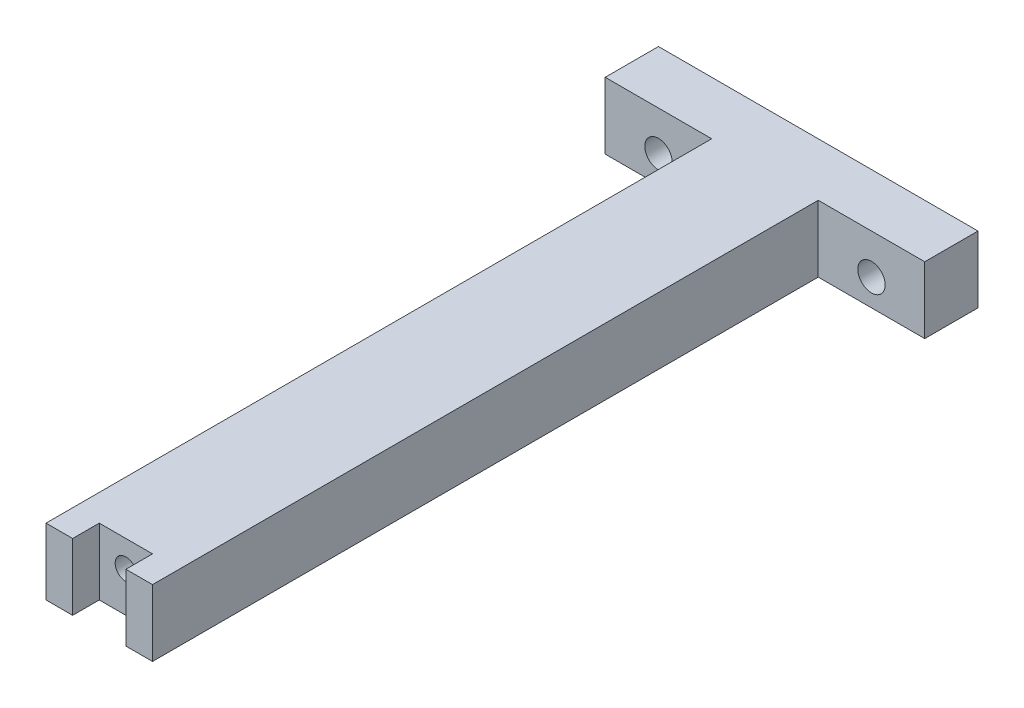
SolidWorks part; units mm, degrees
ref_plane "Front Plane" through (0, 0, 0) normal (0, 0, 1) x (1, 0, 0)
ref_plane "Top Plane" through (0, 0, 0) normal (0, 1, 0) x (1, 0, 0)
ref_plane "Right Plane" through (0, 0, 0) normal (1, 0, 0) x (0, 0, -1)
sketch "Sketch1" plane through (0, 0, 0) normal (0, 0, 1) x (1, 0, 0)
  line L1 (-38.1, -7.9375) -> (38.1, -7.9375)
  line L2 (-38.1, -7.9375) -> (-38.1, 7.9375)
  line L3 (-38.1, 7.9375) -> (38.1, 7.9375)
  line L4 (38.1, -7.9375) -> (38.1, 7.9375)
  line L5 (-38.1, -7.9375) -> (38.1, 7.9375) construction
  line L6 (-38.1, 7.9375) -> (38.1, -7.9375) construction
  point P0 (0, 0)
  dimension "D1" = 76.2
  dimension "D2" = 15.875
extrude "Boss-Extrude1" add sketch "Sketch1" along normal blind 171.45
sketch "Sketch2" plane through (0, 0, 171.45) normal (0, 0, 1) x (1, 0, 0)
  line L0 (-38.1, -7.9375) -> (38.1, -7.9375) construction
  line L1 (-38.1, 7.9375) -> (-12.7, 7.9375)
  line L2 (-38.1, 7.9375) -> (-38.1, -7.9375)
  line L3 (-38.1, -7.9375) -> (-12.7, -7.9375)
  line L4 (-12.7, 7.9375) -> (-12.7, -7.9375)
  line L6 (38.1, 7.9375) -> (12.7, 7.9375)
  line L7 (38.1, 7.9375) -> (38.1, -7.9375)
  line L8 (38.1, -7.9375) -> (12.7, -7.9375)
  line L9 (12.7, 7.9375) -> (12.7, -7.9375)
  dimension "D1" = 12.7
  dimension "D2" = 12.7
extrude "Cut-Extrude1" cut sketch "Sketch2" against normal blind 158.75
sketch "Sketch3" plane through (0, 0, 171.45) normal (0, 0, 1) x (1, 0, 0)
  line L0 (12.7, 7.9375) -> (-12.7, 7.9375) construction
  line L1 (-6.35, -7.9375) -> (6.35, -7.9375)
  line L2 (-6.35, -7.9375) -> (-6.35, 7.9375)
  line L3 (-6.35, 7.9375) -> (6.35, 7.9375)
  line L4 (6.35, -7.9375) -> (6.35, 7.9375)
  line L5 (-6.35, -7.9375) -> (6.35, 7.9375) construction
  line L6 (-6.35, 7.9375) -> (6.35, -7.9375) construction
  point P0 (0, 0)
  dimension "D1" = 12.7
extrude "Cut-Extrude2" cut sketch "Sketch3" against normal blind 6.35
hole_wizard "1/4-20 Tapped Hole1" positions "Sketch4" profile "Sketch5" tap size "1/4-20" standard "ANSI Inch"
sketch "Sketch4" plane through (0, 0, 165.1) normal (0, 0, 1) x (1, 0, 0)
  line L0 (6.35, 7.9375) -> (-6.35, 7.9375) construction
  point P0 (0, 1.5875)
  dimension "D1" = 6.35
cosmetic thread "Hole Thread1" parameters "D1"=7.0104, "D2"=6.35
sketch "Sketch5" plane through (0, 1.5875, 165.1) normal (1, 0, 0) x (0, -1, 0)
  line L0 (0, 0) -> (0, 12.3542)
  line L1 (0, 12.3542) -> (2.5527, 10.8204)
  line L2 (2.5527, 10.8204) -> (2.5527, 0)
  line L5 (2.5527, 0) -> (0, 0)
  line L10 (0, 12.3542) -> (-2.5527, 10.8204) construction
  line L11 (0, -6.35) -> (0, 107.95) construction
  dimension "Tap Drill Dia." = 5.1054
  dimension "Tap Drill Depth" = 10.8204
  dimension "Drill Angle" = 118
sketch "Sketch6" plane through (0, 0, 12.7) normal (0, 0, 1) x (1, 0, 0)
  line L0 (-12.7, 7.9375) -> (-38.1, 7.9375) construction
  line L1 (38.1, 7.9375) -> (12.7, 7.9375) construction
  circle A0 centre (-25.4, -1.5875) radius 3.2639
  circle A1 centre (25.4, -1.5875) radius 3.2639
  dimension "D1" = 6.5278
  dimension "D2" = 6.5278
  dimension "D3" = 25.4
  dimension "D4" = 25.4
  dimension "D5" = 9.525
  dimension "D6" = 9.525
extrude "Cut-Extrude3" cut sketch "Sketch6" against normal through all and the other way through all
